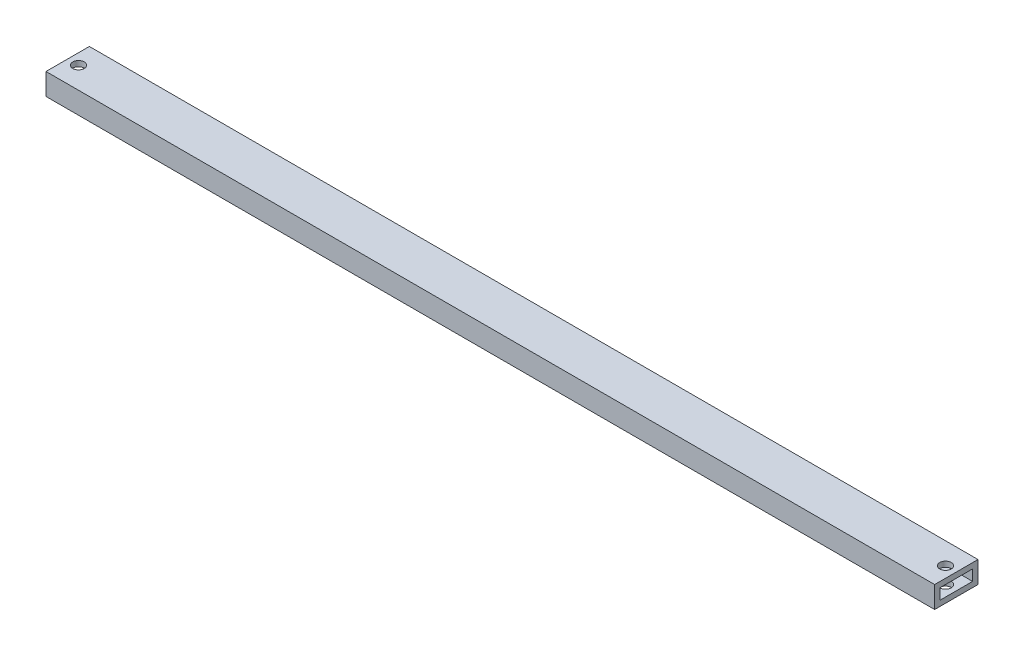
SolidWorks part; units mm, degrees
ref_plane "Front" through (0, 0, 0) normal (0, 0, 1) x (1, 0, 0)
ref_plane "Top" through (0, 0, 0) normal (0, 1, 0) x (1, 0, 0)
ref_plane "Right" through (0, 0, 0) normal (1, 0, 0) x (0, 0, -1)
sketch "Sketch1" plane through (0, 0, 0) normal (1, 0, 0) x (0, 0, -1)
  line L0 (3.175, 9.525) -> (22.225, 9.525)
  line L1 (0, 0) -> (25.4, 0)
  line L2 (0, 0) -> (0, 12.7)
  line L3 (0, 12.7) -> (25.4, 12.7)
  line L4 (25.4, 0) -> (25.4, 12.7)
  line L5 (0, 0) -> (25.4, 12.7) construction
  line L6 (0, 12.7) -> (25.4, 0) construction
  line L7 (22.225, 3.175) -> (22.225, 9.525)
  line L8 (3.175, 3.175) -> (22.225, 3.175)
  line L9 (3.175, 3.175) -> (3.175, 9.525)
  point P4 (12.7, 6.35)
  dimension "D1" = 12.7
  dimension "D2" = 25.4
  dimension "D3" = 3.175
extrude "Boss-Extrude1" add sketch "Sketch1" along normal blind 520.7
sketch "Sketch2" plane through (0, 12.7, 0) normal (0, 1, 0) x (1, 0, 0)
  line L0 (0, 12.7) -> (6.35, 12.7) construction
  line L1 (0, 25.4) -> (0, 0) construction
  line L2 (6.35, 12.7) -> (514.35, 12.7) construction
  line L3 (514.35, 12.7) -> (520.7, 12.7) construction
  line L4 (520.7, 25.4) -> (520.7, 0) construction
  circle A0 centre (6.35, 12.7) radius 3.3528
  circle A1 centre (514.35, 12.7) radius 3.3528
  dimension "D2" = 6.7056
  dimension "D1" = 508
extrude "Cut-Extrude1" cut sketch "Sketch2" against normal through all
